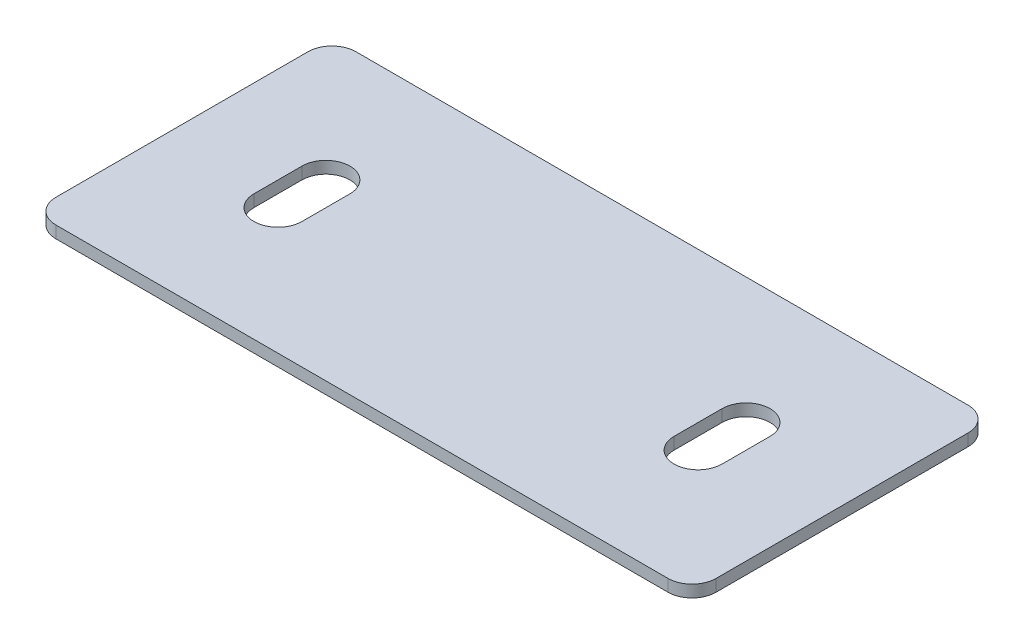
SolidWorks part; units mm, degrees
ref_plane "Спереди" through (0, 0, 0) normal (0, 0, 1) x (1, 0, 0)
ref_plane "Сверху" through (0, 0, 0) normal (0, 1, 0) x (1, 0, 0)
ref_plane "Справа" through (0, 0, 0) normal (1, 0, 0) x (0, 0, -1)
sketch "Эскиз1" plane through (0, 0, 0) normal (0, 1, 0) x (1, 0, 0)
  line L0 (-20.2183, 2.2127) -> (-20.2183, -1.7873) construction
  line L1 (-30.2183, 12.7127) -> (24.7817, 12.7127)
  line L2 (-30.2183, 12.7127) -> (-30.2183, -12.2873)
  line L3 (-30.2183, -12.2873) -> (24.7817, -12.2873)
  line L4 (24.7817, 12.7127) -> (24.7817, -12.2873)
  line L5 (-18.2183, 2.2127) -> (-18.2183, -1.7873)
  line L6 (-22.2183, 2.2127) -> (-22.2183, -1.7873)
  line L7 (-2.7183, 12.7127) -> (-2.7183, -12.2873) construction
  line L8 (14.7817, 2.2127) -> (14.7817, -1.7873) construction
  line L9 (12.7817, 2.2127) -> (12.7817, -1.7873)
  line L10 (16.7817, 2.2127) -> (16.7817, -1.7873)
  arc A0 (-18.2183, 2.2127) -> (-22.2183, 2.2127) centre (-20.2183, 2.2127) ccw
  arc A1 (-22.2183, -1.7873) -> (-18.2183, -1.7873) centre (-20.2183, -1.7873) ccw
  arc A2 (12.7817, 2.2127) -> (16.7817, 2.2127) centre (14.7817, 2.2127) cw
  arc A3 (16.7817, -1.7873) -> (12.7817, -1.7873) centre (14.7817, -1.7873) cw
  point P0 (0, 0)
  point P8 (-20.2183, 0.2127)
  point P13 (-20.2183, 4.2127)
  point P14 (-20.2183, -3.7873)
  point P19 (14.7817, 0.2127)
  dimension "D3" = 8
  dimension "D1" = 55
  dimension "D2" = 25
  dimension "D4" = 10
  dimension "D5" = 12.5
  dimension "D6" = 4
extrude "Бобышка-Вытянуть1" add sketch "Эскиз1" along normal blind 1
fillet "Скругление1" radius 2 4 edges at (-30.2183, 0.5, 12.2873) (-30.2183, 0.5, -12.7127) (24.7817, 0.5, -12.7127) (24.7817, 0.5, 12.2873)
